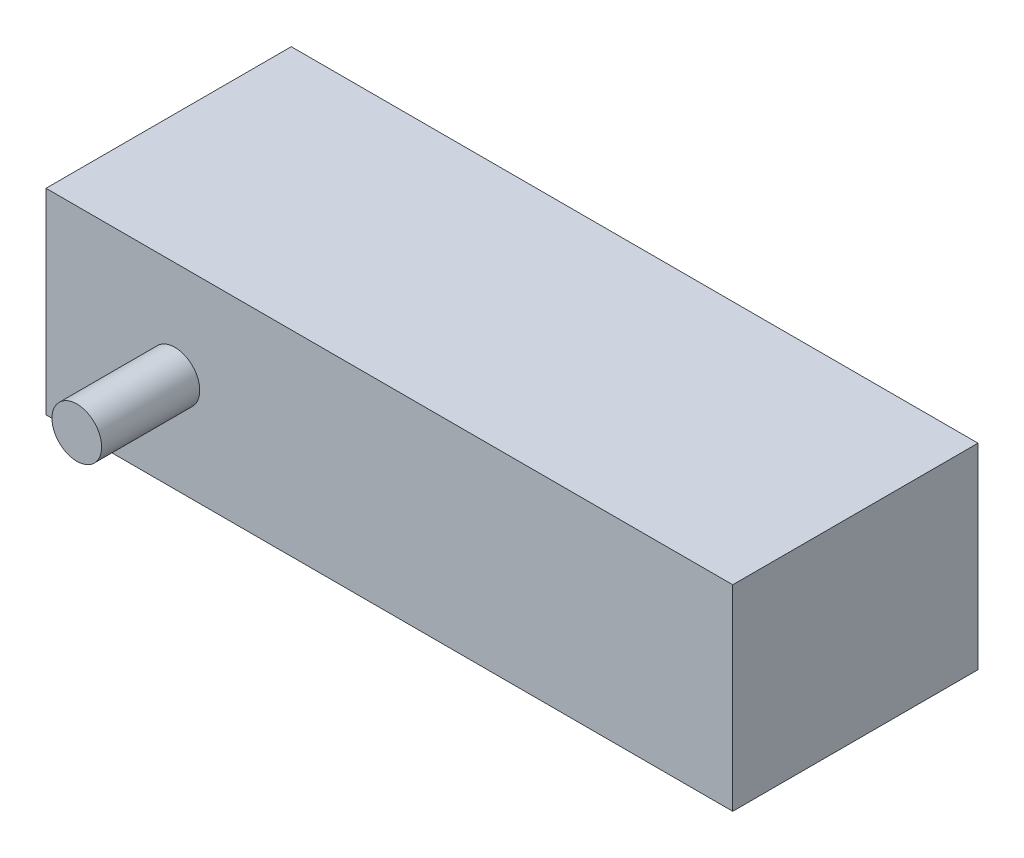
SolidWorks part; units mm, degrees
ref_plane "Front Plane" through (0, 0, 0) normal (0, 0, 1) x (1, 0, 0)
ref_plane "Top Plane" through (0, 0, 0) normal (0, 1, 0) x (1, 0, 0)
ref_plane "Right Plane" through (0, 0, 0) normal (1, 0, 0) x (0, 0, -1)
sketch "Sketch1" plane through (0, 0, 0) normal (0, 1, 0) x (1, 0, 0)
  line L1 (-35, -12.5) -> (35, -12.5)
  line L2 (-35, -12.5) -> (-35, 12.5)
  line L3 (-35, 12.5) -> (35, 12.5)
  line L4 (35, -12.5) -> (35, 12.5)
  line L5 (-35, -12.5) -> (35, 12.5) construction
  line L6 (-35, 12.5) -> (35, -12.5) construction
  point P0 (0, 0)
  dimension "D1" = 70
  dimension "D2" = 25
extrude "Boss-Extrude1" add sketch "Sketch1" along normal blind 20
sketch "Sketch2" plane through (0, 0, 12.5) normal (0, 0, 1) x (1, 0, 0)
  circle A0 centre (-21.8588, 10) radius 2.5317
  dimension "D1" = 10
extrude "Boss-Extrude2" add sketch "Sketch2" along normal blind 10
